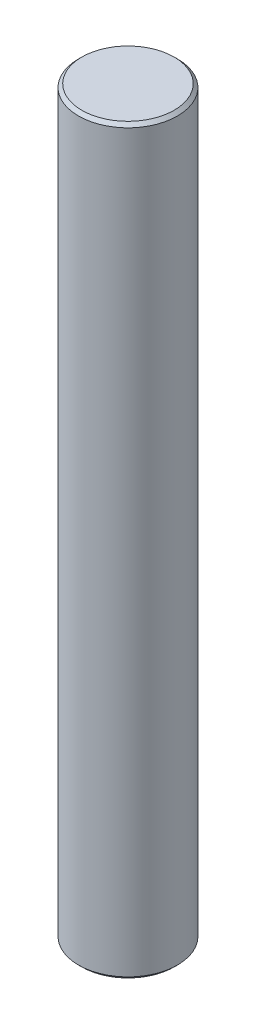
SolidWorks part; units mm, degrees
ref_plane "Front Plane" through (0, 0, 0) normal (0, 0, 1) x (1, 0, 0)
ref_plane "Top Plane" through (0, 0, 0) normal (0, 1, 0) x (1, 0, 0)
ref_plane "Right Plane" through (0, 0, 0) normal (1, 0, 0) x (0, 0, -1)
sketch "Sketch1" plane through (0, 0, 0) normal (0, 0, 1) x (1, 0, 0)
  line L0 (0, 72.7086) -> (0, -88.66) construction
  line L1 (-37.6527, 0) -> (68.8135, 0) construction
  line L2 (0, 22.5) -> (3, 22.5)
  line L3 (0, 22.5) -> (0, -22.5)
  line L4 (0, -22.5) -> (3, -22.5)
  line L5 (3, 22.5) -> (3, -22.5)
  dimension "D1" = 6
  dimension "D2" = 45
revolve "Revolve1" add sketch "Sketch1" angle 360 about L0
chamfer "Chamfer1" distance 0.2 angle 45 2 edges at (0, -22.5, 3) (0, 22.5, 3)
